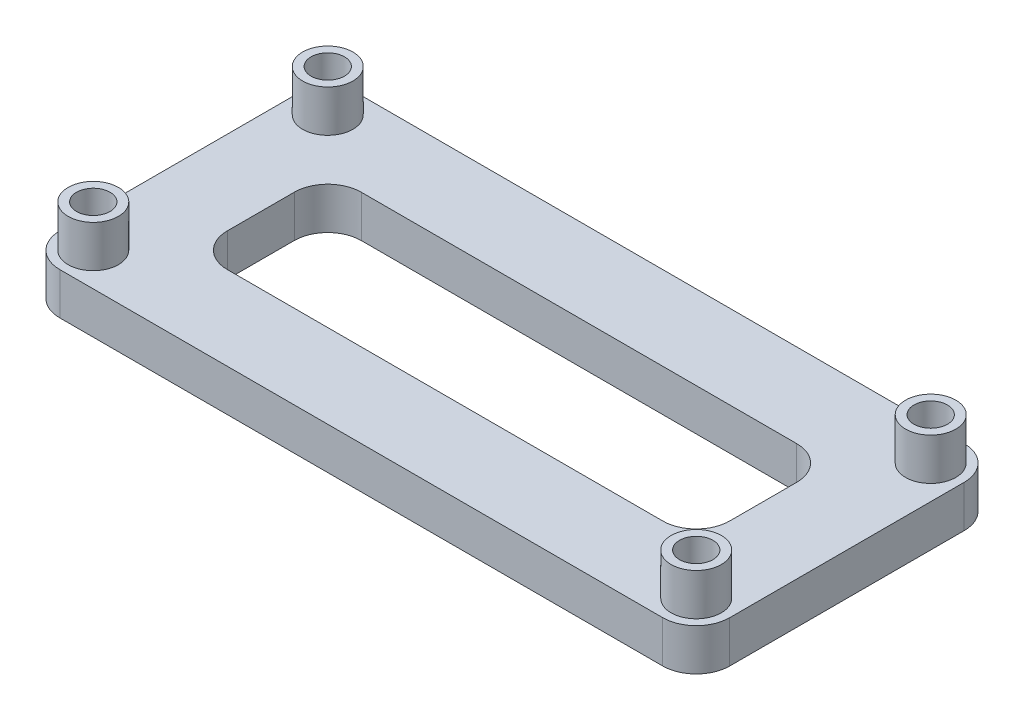
SolidWorks part; units mm, degrees
ref_plane "Front Plane" through (0, 0, 0) normal (0, 0, 1) x (1, 0, 0)
ref_plane "Top Plane" through (0, 0, 0) normal (0, 1, 0) x (1, 0, 0)
ref_plane "Right Plane" through (0, 0, 0) normal (1, 0, 0) x (0, 0, -1)
sketch "Sketch1" plane through (0, 0, 0) normal (0, 1, 0) x (1, 0, 0)
  line L1 (0, 0) -> (50.8, 0)
  line L2 (0, 0) -> (0, 22.86)
  line L3 (0, 22.86) -> (50.8, 22.86)
  line L4 (50.8, 0) -> (50.8, 22.86)
  line L5 (6.35, 16.51) -> (44.45, 16.51)
  line L6 (6.35, 16.51) -> (6.35, 6.35)
  line L7 (6.35, 6.35) -> (44.45, 6.35)
  line L8 (44.45, 16.51) -> (44.45, 6.35)
  circle A0 centre (2.54, 20.32) radius 1.27
  circle A1 centre (48.26, 20.32) radius 1.27
  circle A2 centre (2.54, 2.54) radius 1.27
  circle A3 centre (48.26, 2.54) radius 1.27
  dimension "D3" = 2.54
  dimension "D4" = 2.54
  dimension "D5" = 2.54
  dimension "D6" = 2.54
  dimension "D1" = 22.86
  dimension "D2" = 50.8
  dimension "D7" = 45.72
  dimension "D8" = 17.78
  dimension "D9" = 2.54
  dimension "D10" = 2.54
  dimension "D11" = 6.35
  dimension "D12" = 38.1
  dimension "D13" = 6.35
  dimension "D14" = 10.16
extrude "Boss-Extrude1" add sketch "Sketch1" along normal blind 3.175
sketch "Sketch2" plane through (0, 3.175, 0) normal (0, 1, 0) x (1, 0, 0)
  line L0 (0, 11.43) -> (50.8, 11.43) construction
  line L1 (0, 22.86) -> (0, 0) construction
  line L2 (50.8, 0) -> (50.8, 22.86) construction
  line L3 (25.4, 22.86) -> (25.4, 0) construction
  line L4 (50.8, 22.86) -> (0, 22.86) construction
  line L5 (0, 0) -> (50.8, 0) construction
  circle A0 centre (2.54, 20.32) radius 1.905
  circle A1 centre (2.54, 20.32) radius 1.27
  circle A2 centre (2.54, 2.54) radius 1.27
  circle A3 centre (2.54, 2.54) radius 1.905
  circle A4 centre (48.26, 2.54) radius 1.27
  circle A5 centre (48.26, 2.54) radius 1.905
  circle A6 centre (48.26, 20.32) radius 1.27
  circle A7 centre (48.26, 20.32) radius 1.905
  dimension "D1" = 3.81
  dimension "D2" = 2.54
extrude "Boss-Extrude2" add sketch "Sketch2" along normal blind 3.175
fillet "Fillet1" radius 2.54 8 edges at (50.8, 1.5875, 0) (50.8, 1.5875, -22.86) (0, 1.5875, -22.86) (0, 1.5875, 0) (6.35, 1.5875, -6.35) (44.45, 1.5875, -6.35) (44.45, 1.5875, -16.51) (6.35, 1.5875, -16.51)
equation "\"D4@Sketch1\"=\"D3@Sketch1\""
equation "\"D5@Sketch1\"=\"D3@Sketch1\""
equation "\"D6@Sketch1\"=\"D3@Sketch1\""
equation "\"D9@Sketch1\"=(\"D1@Sketch1\"-\"D8@Sketch1\")/2"
equation "\"D10@Sketch1\"=(\"D2@Sketch1\"-\"D7@Sketch1\")/2"
